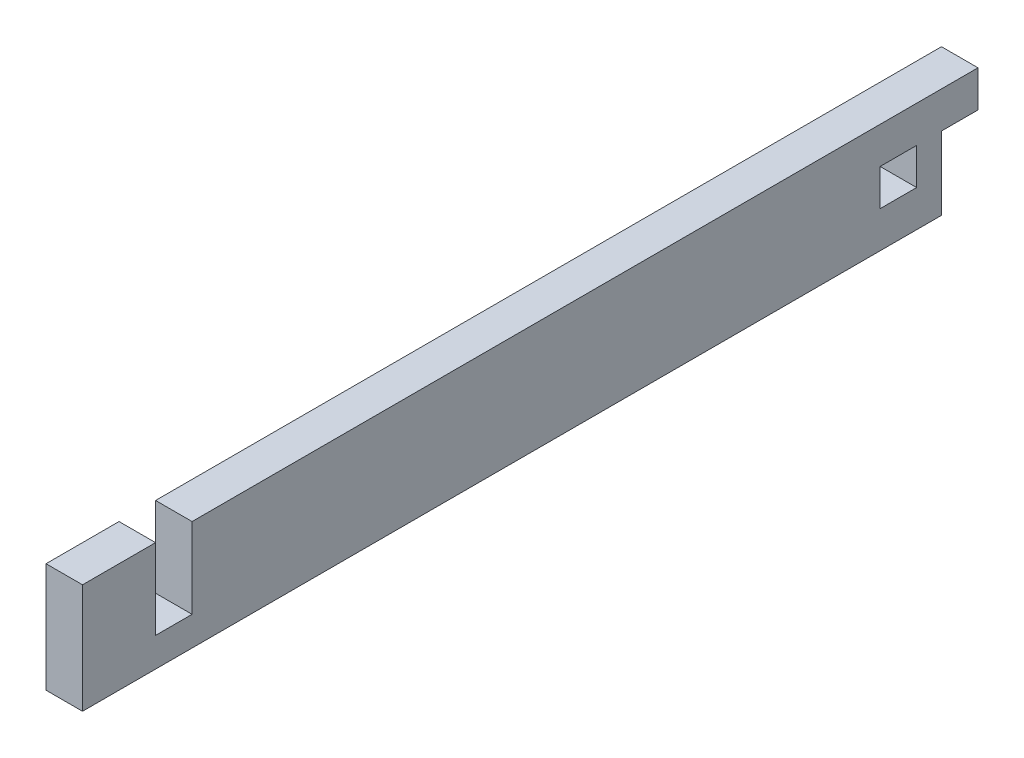
SolidWorks part; units mm, degrees
material "Acrylic (Medium-high impact)"
ref_plane "Front" through (0, 0, 0) normal (0, 0, 1) x (1, 0, 0)
ref_plane "Bottom" through (0, 0, 0) normal (0, 1, 0) x (1, 0, 0)
ref_plane "Right" through (0, 0, 0) normal (1, 0, 0) x (0, 0, -1)
sketch "Sketch1" plane through (0, 0, 0) normal (0, 1, 0) x (1, 0, 0)
  line L0 (-10.033, 66.167) -> (-11.6205, 66.167)
  line L2 (-11.6205, -66.167) -> (11.6205, -66.167)
  line L4 (11.6205, 66.167) -> (10.033, 66.167)
  line L5 (10.033, 66.167) -> (10.033, 59.817)
  line L6 (10.033, 59.817) -> (11.6205, 59.817)
  line L7 (11.6205, 59.817) -> (11.6205, -59.817)
  line L8 (11.6205, -59.817) -> (-11.6205, -59.817)
  line L9 (-11.6205, -59.817) -> (-11.6205, 59.817)
  line L10 (-11.6205, 59.817) -> (-10.033, 59.817)
  line L11 (-10.033, 59.817) -> (-10.033, 66.167)
  line L12 (-17.9705, -78.867) -> (-17.9705, 76.835)
  line L13 (-17.9705, 76.835) -> (-11.6205, 76.835)
  line L14 (-11.6205, 76.835) -> (-11.6205, 66.167)
  line L15 (11.6205, 66.167) -> (11.6205, 76.835)
  line L16 (11.6205, 76.835) -> (17.9705, 76.835)
  line L17 (17.9705, 76.835) -> (17.9705, -78.867)
  line L21 (-17.9705, -78.867) -> (-11.6205, -78.867)
  line L22 (-11.6205, -66.167) -> (-11.6205, -78.867)
  line L25 (17.9705, -78.867) -> (11.6205, -78.867)
  line L26 (11.6205, -66.167) -> (11.6205, -78.867)
  point P12 (0, -59.817)
  point P13 (-11.6205, 0)
  point P25 (-10.8267, 59.817)
  dimension "D1" = 6.35
  dimension "D2" = 6.35
  dimension "D3" = 6.35
  dimension "D4" = 1.5875
  dimension "D5" = 17.018
  dimension "D6" = 23.241
  dimension "D7" = 119.634
  dimension "D8" = 12.7
extrude "Boss-Extrude1" add sketch "Sketch1" along normal blind 19.05
sketch "Sketch2" plane through (-17.9705, 0, 0) normal (-1, 0, 0) x (0, 0, 1)
  line L0 (-76.835, 19.05) -> (78.867, 19.05) construction
  line L1 (8.255, 19.05) -> (51.689, 19.05)
  line L2 (8.255, 19.05) -> (8.255, 5.08)
  line L3 (8.255, 5.08) -> (51.689, 5.08)
  line L4 (51.689, 19.05) -> (51.689, 5.08)
  line L6 (-76.835, 0) -> (78.867, 0) construction
  dimension "D1" = 8.128
  dimension "D2" = 51.562
  dimension "D3" = 5.08
extrude "Motor Hole" cut sketch "Sketch2" against normal blind 19.05
sketch "Sketch3" plane through (-17.9705, 0, 0) normal (-1, 0, 0) x (0, 0, 1)
  line L0 (-76.835, 19.05) -> (-76.835, 0) construction
  line L1 (-76.835, 0) -> (-70.485, 0)
  line L2 (-76.835, 0) -> (-76.835, 12.7)
  line L3 (-76.835, 12.7) -> (-70.485, 12.7)
  line L4 (-70.485, 0) -> (-70.485, 12.7)
  line L6 (-76.835, 0) -> (78.867, 0) construction
  dimension "D1" = 12.7
  dimension "D2" = 6.35
extrude "Cut-Extrude2" cut sketch "Sketch3" against normal through all
sketch "Sketch5" plane through (-17.9705, 0, 0) normal (-1, 0, 0) x (0, 0, 1)
  line L0 (51.689, 19.05) -> (78.867, 19.05) construction
  line L1 (59.817, 19.05) -> (66.167, 19.05)
  line L2 (59.817, 19.05) -> (59.817, 5.08)
  line L3 (59.817, 5.08) -> (66.167, 5.08)
  line L4 (66.167, 19.05) -> (66.167, 5.08)
  line L5 (8.255, 5.08) -> (51.689, 5.08) construction
  line L6 (78.867, 19.05) -> (78.867, 0) construction
  line L7 (-66.167, 12.7) -> (-59.817, 12.7)
  line L8 (-66.167, 12.7) -> (-66.167, 6.35)
  line L9 (-66.167, 6.35) -> (-59.817, 6.35)
  line L10 (-59.817, 12.7) -> (-59.817, 6.35)
  point P18 (-66.167, 9.525)
  point P21 (78.867, 9.525)
  dimension "D1" = 6.35
extrude "Cut-Extrude6" cut sketch "Sketch5" against normal through all
sketch "Sketch7" plane through (0, 0, 0) normal (0, 1, 0) x (1, 0, 0)
  line L1 (11.6205, -78.867) -> (-34.3558, -78.867)
  line L2 (11.6205, -78.867) -> (11.6205, 80.9204)
  line L3 (11.6205, 80.9204) -> (-34.3558, 80.9204)
  line L4 (-34.3558, -78.867) -> (-34.3558, 80.9204)
extrude "Cut-Extrude7" cut sketch "Sketch7" along normal through all
